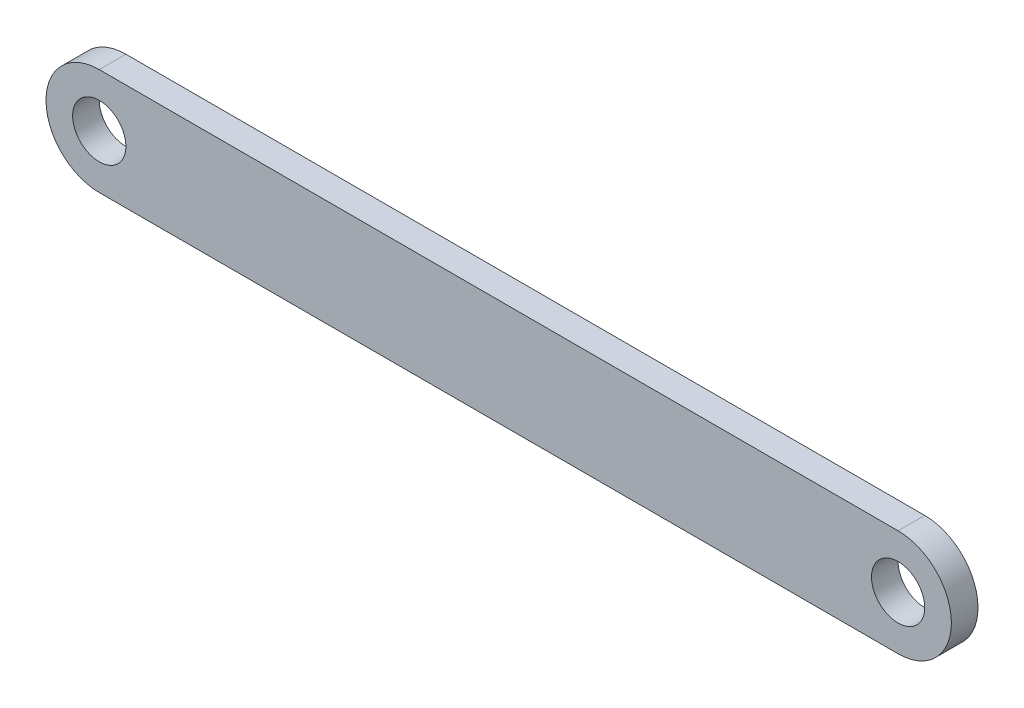
SolidWorks part; units mm, degrees
ref_plane "Front Plane" through (0, 0, 0) normal (0, 0, 1) x (1, 0, 0)
ref_plane "Top Plane" through (0, 0, 0) normal (0, 1, 0) x (1, 0, 0)
ref_plane "Right Plane" through (0, 0, 0) normal (1, 0, 0) x (0, 0, -1)
sketch "Sketch1" plane through (0, 0, 0) normal (0, 0, 1) x (1, 0, 0)
  line L0 (0, -8.8018) -> (-76.2, -8.8018) construction
  line L1 (0, -13.8818) -> (-76.2, -13.8818)
  line L2 (0, -3.7218) -> (-76.2, -3.7218)
  arc A0 (0, -13.8818) -> (0, -3.7218) centre (0, -8.8018) ccw
  arc A1 (-76.2, -3.7218) -> (-76.2, -13.8818) centre (-76.2, -8.8018) ccw
  circle A2 centre (-76.2, -8.8018) radius 2.54
  circle A3 centre (0, -8.8018) radius 2.54
  point P2 (-38.1, -8.8018)
  dimension "D2" = 5.08
  dimension "D3" = 5.08
  dimension "D4" = 5.08
  dimension "D1" = 76.2
extrude "Boss-Extrude1" add sketch "Sketch1" along normal blind 2.54
